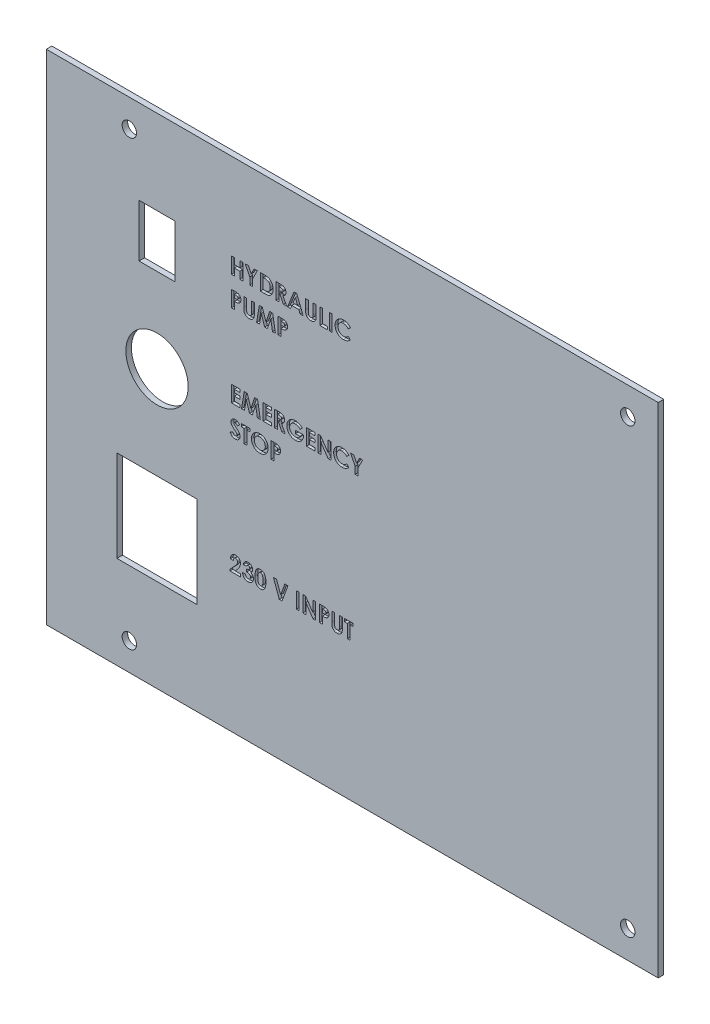
SolidWorks part; units mm, degrees
ref_plane "Front Plane" through (0, 0, 0) normal (0, 0, 1) x (1, 0, 0)
ref_plane "Top Plane" through (0, 0, 0) normal (0, 1, 0) x (1, 0, 0)
ref_plane "Right Plane" through (0, 0, 0) normal (1, 0, 0) x (0, 0, -1)
sketch "Sketch1" plane through (0, 0, 0) normal (0, 0, 1) x (1, 0, 0)
  line L0 (120, 80) -> (-120, 80) construction
  line L1 (-120, -90) -> (120, -90)
  line L2 (-120, -90) -> (-120, 90)
  line L3 (-120, 90) -> (120, 90)
  line L4 (120, -90) -> (120, 90)
  line L5 (-120, -90) -> (120, 90) construction
  line L6 (-120, 90) -> (120, -90) construction
  line L7 (-110, 90) -> (-110, -88.3577) construction
  line L8 (0, 90) -> (0, -90) construction
  line L9 (-120, 0) -> (120, 0) construction
  circle A0 centre (-90, 80) radius 2.6
  circle A1 centre (-110, 70) radius 2.6 construction
  circle A2 centre (90, 80) radius 2.6
  circle A3 centre (-90, -80) radius 2.6
  circle A4 centre (90, -80) radius 2.6
  circle A5 centre (-110, -70) radius 2.6 construction
  point P0 (0, 0)
  dimension "D5" = 5.2
  dimension "D7" = 5.2
  dimension "D1" = 240
  dimension "D2" = 180
  dimension "D3" = 10
  dimension "D4" = 10
  dimension "D6" = 30
  dimension "D8" = 20
extrude "Boss-Extrude1" add sketch "Sketch1" along normal blind 2
sketch "Sketch2" plane through (0, 0, 2) normal (0, 0, 1) x (1, 0, 0)
  line L0 (-80, 10) -> (-80, -40) construction
  line L1 (-53.813, 72.6036) -> (-53.813, -66.9571) construction
  line L2 (-94.5, -56.5) -> (-65.5, -56.5)
  line L3 (-94.5, -56.5) -> (-94.5, -23.5)
  line L4 (-94.5, -23.5) -> (-65.5, -23.5)
  line L5 (-65.5, -56.5) -> (-65.5, -23.5)
  line L6 (-94.5, -56.5) -> (-65.5, -23.5) construction
  line L7 (-94.5, -23.5) -> (-65.5, -56.5) construction
  line L9 (-120, 90) -> (-120, -90) construction
  line L10 (-120, -90) -> (120, -90) construction
  line L11 (-80, 10) -> (-80, 50) construction
  line L13 (-86.5, 59.5) -> (-73.5, 59.5)
  line L14 (-86.5, 59.5) -> (-86.5, 40.5)
  line L15 (-86.5, 40.5) -> (-73.5, 40.5)
  line L16 (-73.5, 59.5) -> (-73.5, 40.5)
  line L17 (-86.5, 59.5) -> (-73.5, 40.5) construction
  line L18 (-86.5, 40.5) -> (-73.5, 59.5) construction
  circle A0 centre (-80, 10) radius 11.25
  text T0 "<b>HYDRAULIC </b>\r\n<b>PUMP</b>" font "Century Gothic" height in points 22
  text T1 "<b>EMERGENCY</b>\r\n<b>STOP</b>" font "Century Gothic" height in points 22
  text T2 "<b>230 V INPUT</b>" font "Century Gothic" height in points 22
  point P2 (-80, 50)
  point P4 (-80, -40)
  point P18 (-80, 40.5)
  dimension "D1" = 22.5
  dimension "D7" = 13
  dimension "D2" = 29
  dimension "D3" = 33
  dimension "D4" = 50
  dimension "D5" = 40
  dimension "D6" = 50
  dimension "D8" = 19
  dimension "D9" = 40
extrude "Cut-Extrude1" cut sketch "Sketch2" against normal offset from surface (1 mm away) 1 up to face at (-92.6, -80, 0)
sketch "Sketch3" plane through (0, 0, 1) normal (0, 0, 1) x (1, 0, 0)
  line L4 (-73.5, 40.5) -> (-73.5, 59.5)
  line L5 (-73.5, 59.5) -> (-86.5, 59.5)
  line L6 (-86.5, 59.5) -> (-86.5, 40.5)
  line L7 (-86.5, 40.5) -> (-73.5, 40.5)
  line L8 (-73.5, 40.5) -> (-73.5, 59.5)
  line L9 (-73.5, 59.5) -> (-86.5, 59.5)
  line L10 (-86.5, 59.5) -> (-86.5, 40.5)
  line L11 (-86.5, 40.5) -> (-73.5, 40.5)
  line L12 (-65.5, -56.5) -> (-65.5, -23.5)
  line L13 (-65.5, -23.5) -> (-94.5, -23.5)
  line L14 (-94.5, -23.5) -> (-94.5, -56.5)
  line L15 (-94.5, -56.5) -> (-65.5, -56.5)
  line L16 (-65.5, -56.5) -> (-65.5, -23.5)
  line L17 (-65.5, -23.5) -> (-94.5, -23.5)
  line L18 (-94.5, -23.5) -> (-94.5, -56.5)
  line L19 (-94.5, -56.5) -> (-65.5, -56.5)
  circle A1 centre (-80, 10) radius 11.25
  circle A2 centre (-80, 10) radius 11.25
  dimension "D1" = 0
  dimension "D2" = 0
  dimension "D3" = 0
extrude "Cut-Extrude2" cut sketch "Sketch3" against normal blind 10
sketch "Sketch4" plane through (0, 0, 2) normal (0, 0, 1) x (1, 0, 0)
  line L0 (-120, -90) -> (120, -90) construction
  line L1 (120, 90) -> (101, 90)
  line L2 (120, 90) -> (120, -90)
  line L3 (120, -90) -> (101, -90)
  line L4 (101, 90) -> (101, -90)
  line L5 (-120, 90) -> (-120, -90) construction
  dimension "D1" = 221
extrude "Cut-Extrude3" cut sketch "Sketch4" against normal blind 10
